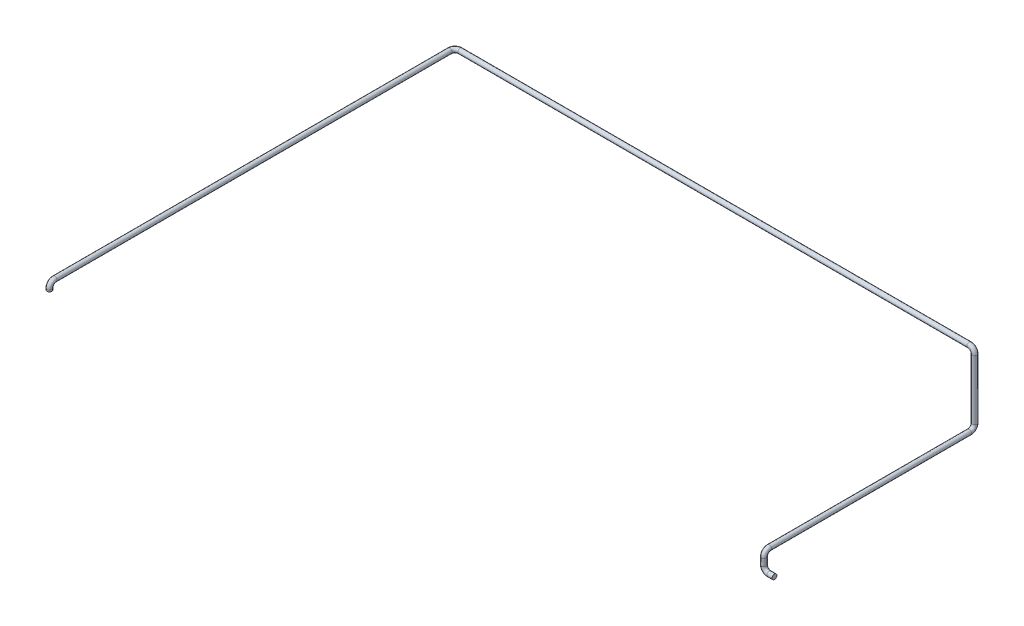
SolidWorks part; units mm, degrees
ref_plane "Alzado" through (0, 0, 0) normal (0, 0, 1) x (1, 0, 0)
ref_plane "Planta" through (0, 0, 0) normal (0, 1, 0) x (1, 0, 0)
ref_plane "Vista lateral" through (0, 0, 0) normal (1, 0, 0) x (0, 0, -1)
sketch3d "Croquis3D1"
  line L0 (0, 0, 0) -> (-30, 0, 0)
  line L1 (-60, 30, 0) -> (-60, 70, 0)
  line L2 (-60, 100, -30) -> (-60, 100, -1170)
  line L6 (-60, 130, -1200) -> (-60, 470, -1200)
  line L7 (-90, 500, -1200) -> (-2990, 500, -1200)
  line L8 (-3020, 500, -1170) -> (-3020, 500, 1080)
  line L9 (-3020, 470, 1110) -> (-3020, 460, 1110)
  arc A0 (-3020, 500, 1080) -> (-3020, 470, 1110) centre (-3020, 470, 1080) ccw
  arc A1 (-2990, 500, -1200) -> (-3020, 500, -1170) centre (-2990, 500, -1170) ccw
  arc A2 (-60, 470, -1200) -> (-90, 500, -1200) centre (-90, 470, -1200) ccw
  arc A3 (-60, 130, -1200) -> (-60, 100, -1170) centre (-60, 130, -1170) ccw
  arc A4 (-60, 70, 0) -> (-60, 100, -30) centre (-60, 70, -30) ccw
  arc A5 (-30, 0, 0) -> (-60, 30, 0) centre (-30, 30, 0) ccw
  point P6 (-3020, 500, 1110)
  point P11 (-2990, 470, 1080)
  point P15 (-3020, 500, -1200)
  point P16 (-2990, 530, -1170)
  point P19 (-60, 500, -1200)
  point P20 (-90, 470, -1170)
  point P23 (-60, 100, -1200)
  point P24 (-90, 130, -1170)
  point P27 (-60, 100, 0)
  point P28 (-90, 70, -30)
  point P31 (-60, 0, 0)
  point P32 (-30, 30, -30)
  dimension "D8" = 30
  dimension "D1" = 60
  dimension "D2" = 100
  dimension "D3" = 1200
  dimension "D4" = 400
  dimension "D5" = 2960
  dimension "D6" = 2310
  dimension "D7" = 40
sketch "Croquis1" plane through (0, 0, 0) normal (1, 0, 0) x (0, 0, -1)
  circle A0 centre (0, 0) radius 13.7
  dimension "D1" = 27.4
sweep "Barrer1" add profiles "Croquis1" path "Croquis3D1"
